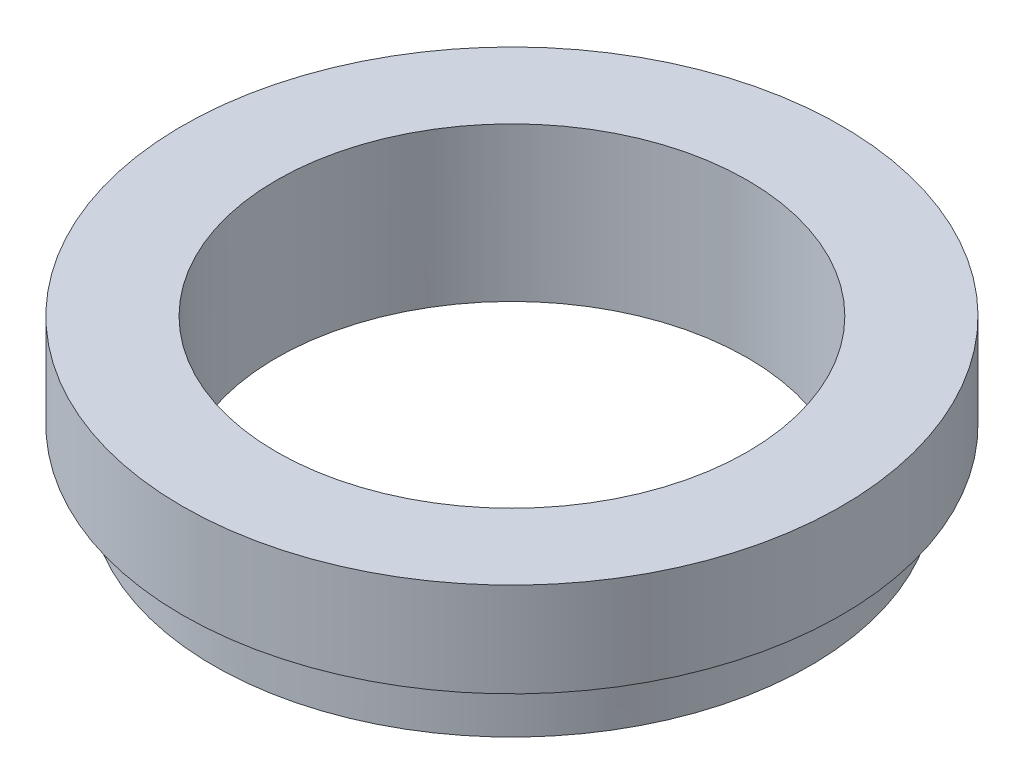
SolidWorks part; units mm, degrees
ref_plane "Piano frontale" through (0, 0, 0) normal (0, 0, 1) x (1, 0, 0)
ref_plane "Piano superiore" through (0, 0, 0) normal (0, 1, 0) x (1, 0, 0)
ref_plane "Piano destro" through (0, 0, 0) normal (1, 0, 0) x (0, 0, -1)
sketch "Schizzo1" plane through (0, 0, 0) normal (0, 1, 0) x (1, 0, 0)
  circle A0 centre (0, 0) radius 9.5
  circle A1 centre (0, 0) radius 7.5
  dimension "D1" = 19
  dimension "D2" = 15
extrude "Estrusione-Estrusione1" add sketch "Schizzo1" along normal blind 5
sketch "Schizzo2" plane through (0, 5, 0) normal (0, 1, 0) x (1, 0, 0)
  circle A0 centre (0, 0) radius 9.5
  circle A1 centre (0, 0) radius 10.5
  dimension "D1" = 21
extrude "Estrusione-Estrusione2" add sketch "Schizzo2" against normal blind 3
sketch "Schizzo3" plane through (0, 0, 0) normal (0, -1, 0) x (1, 0, 0)
  circle A0 centre (0, 0) radius 9.5
extrude "Taglio-Estrusione1" cut sketch "Schizzo3" against normal blind 0.1
